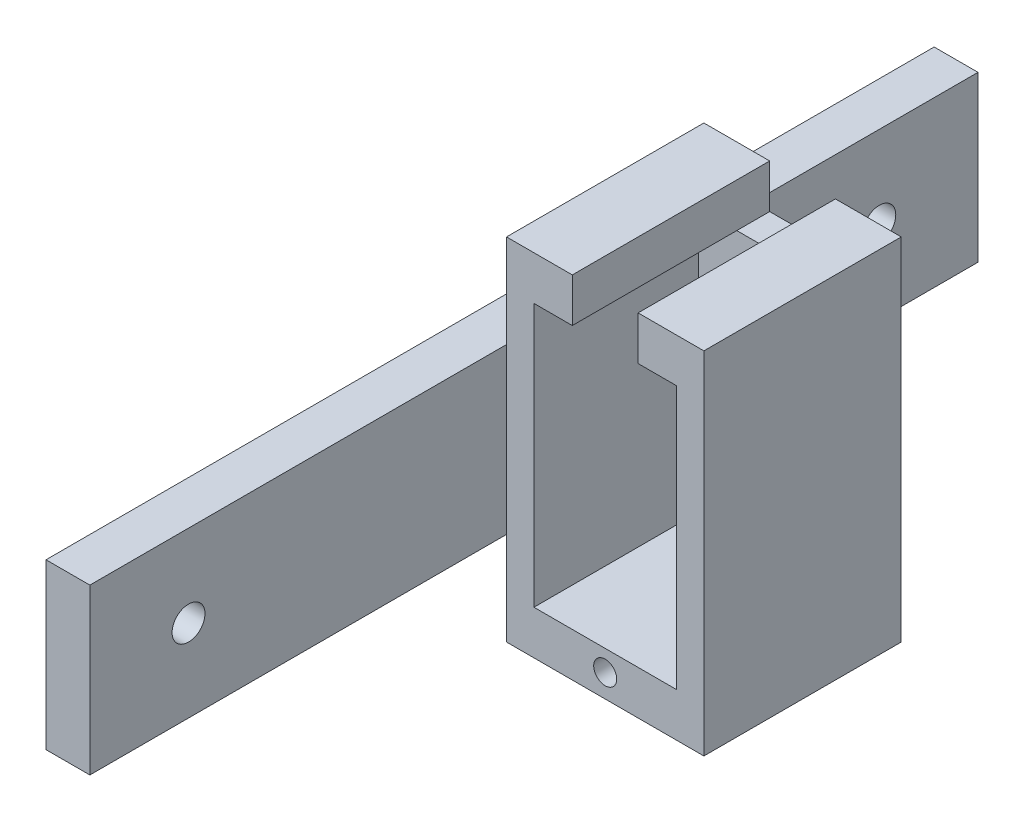
SolidWorks part; units mm, degrees
ref_plane "Plan de face" through (0, 0, 0) normal (0, 0, 1) x (1, 0, 0)
ref_plane "Plan de dessus" through (0, 0, 0) normal (0, 1, 0) x (1, 0, 0)
ref_plane "Plan de droite" through (0, 0, 0) normal (1, 0, 0) x (0, 0, -1)
sketch "Esquisse1" plane through (0, 0, 0) normal (0, 0, 1) x (1, 0, 0)
  line L0 (-12, 32) -> (-12, 28)
  line L1 (0, 0) -> (-18, 0)
  line L2 (0, 0) -> (0, 32)
  line L4 (-18, 0) -> (-18, 32)
  line L5 (-12, 28) -> (-6, 28)
  line L6 (-6, 28) -> (-6, 32)
  line L7 (-12, 32) -> (-18, 32)
  line L8 (-6, 32) -> (0, 32)
  line L9 (-9, 0) -> (-9, 32) construction
  line L10 (-12, 32) -> (-6, 32) construction
  point P12 (-9, 32)
  dimension "D1" = 18
  dimension "D2" = 32
  dimension "D3" = 4
  dimension "D4" = 6
extrude "Boss.-Extru.1" add sketch "Esquisse1" along normal blind 3
sketch "Esquisse2" plane through (0, 0, 3) normal (0, 0, 1) x (1, 0, 0)
  line L3 (-18, 0) -> (0, 0)
  line L7 (-6, 28) -> (-2.5, 28)
  line L8 (-2.5, 28) -> (-2.5, 4)
  line L9 (-2.5, 4) -> (-15.5, 4)
  line L10 (-15.5, 4) -> (-15.5, 28)
  line L11 (-15.5, 28) -> (-12, 28)
  line L13 (-18, 0) -> (-18, 32)
  line L14 (-18, 32) -> (-12, 32)
  line L15 (-12, 32) -> (-12, 28)
  line L16 (-6, 28) -> (-6, 32)
  line L17 (-6, 32) -> (0, 32)
  line L18 (0, 32) -> (0, 0)
  dimension "D1" = 4
  dimension "D2" = 4
  dimension "D3" = 4
  dimension "D4" = 3.5
  dimension "D5" = 3.5
extrude "Boss.-Extru.2" add sketch "Esquisse2" along normal blind 15
sketch "Esquisse3" plane through (0, 0, 18) normal (0, 0, 1) x (1, 0, 0)
  line L0 (-9, 4) -> (-9, 0) construction
  line L1 (-2.5, 4) -> (-15.5, 4) construction
  line L2 (-18, 0) -> (0, 0) construction
  circle A0 centre (-9, 2.1) radius 1.05
  dimension "D1" = 2.1
  dimension "D2" = 1.9
extrude "Enlèv. mat.-Extru.1" cut sketch "Esquisse3" against normal blind 6
sketch "Esquisse4" plane through (-18, 0, 0) normal (-1, 0, 0) x (0, 0, 1)
  line L0 (0, 16) -> (18, 16) construction
  line L1 (-25, 23.5) -> (56, 23.5)
  line L2 (-25, 23.5) -> (-25, 8.5)
  line L3 (-25, 8.5) -> (56, 8.5)
  line L4 (56, 23.5) -> (56, 8.5)
  line L5 (18, 32) -> (18, 0) construction
  line L6 (0, 32) -> (18, 0) construction
  line L7 (18, 32) -> (0, 0) construction
  line L8 (0, 32) -> (0, 0) construction
  line L9 (-25, 16) -> (56, 16) construction
  dimension "D1" = 25
  dimension "D2" = 15
  dimension "D3" = 38
extrude "Boss.-Extru.3" add sketch "Esquisse4" along normal blind 4
sketch "Esquisse5" plane through (-22, 0, 0) normal (-1, 0, 0) x (0, 0, 1)
  line L0 (9, 23.5) -> (9, 8.5) construction
  line L1 (18, 23.5) -> (0, 23.5) construction
  line L2 (0, 8.5) -> (18, 8.5) construction
  line L3 (-25, 16) -> (56, 16) construction
  line L4 (-25, 23.5) -> (-25, 8.5) construction
  line L5 (56, 8.5) -> (56, 23.5) construction
  circle A0 centre (-16, 16) radius 1.5
  circle A1 centre (47, 16) radius 1.5
  dimension "D1" = 3
  dimension "D2" = 3
  dimension "D3" = 9
  dimension "D4" = 9
extrude "Enlèv. mat.-Extru.2" cut sketch "Esquisse5" against normal blind 4
